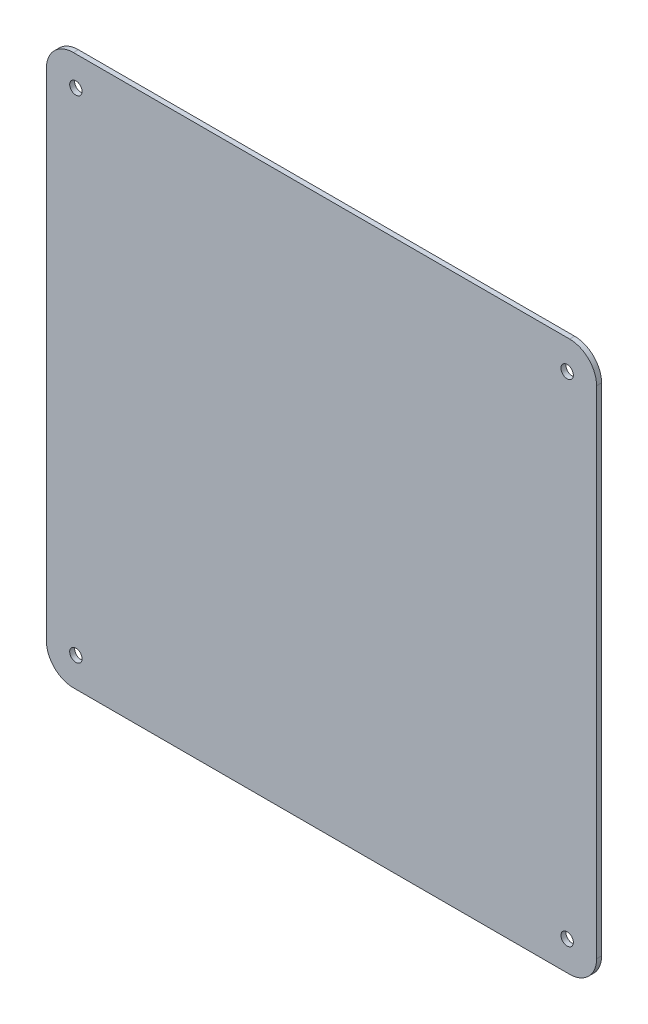
SolidWorks part; units mm, degrees
ref_plane "Piano frontale" through (0, 0, 0) normal (0, 0, 1) x (1, 0, 0)
ref_plane "Piano superiore" through (0, 0, 0) normal (0, 1, 0) x (1, 0, 0)
ref_plane "Piano destro" through (0, 0, 0) normal (1, 0, 0) x (0, 0, -1)
sketch "Sketch1" plane through (0, 0, 0) normal (0, 0, 1) x (1, 0, 0)
  line L4 (-80, 89.2) -> (80, 89.2) construction
  line L5 (89.2, 80) -> (89.2, -80) construction
  line L6 (80, -89.2) -> (-80, -89.2) construction
  line L7 (-89.2, -80) -> (-89.2, 80) construction
  line L8 (-80, 88.7) -> (80, 88.7)
  line L9 (88.7, 80) -> (88.7, -80)
  line L10 (80, -88.7) -> (-80, -88.7)
  line L11 (-88.7, -80) -> (-88.7, 80)
  arc A10 (-80, 89.2) -> (-89.2, 80) centre (-80, 80) ccw construction
  arc A13 (89.2, 80) -> (80, 89.2) centre (80, 80) ccw construction
  arc A14 (80, -89.2) -> (89.2, -80) centre (80, -80) ccw construction
  arc A15 (-89.2, -80) -> (-80, -89.2) centre (-80, -80) ccw construction
  arc A16 (88.7, 80) -> (80, 88.7) centre (80, 80) ccw
  arc A17 (80, -88.7) -> (88.7, -80) centre (80, -80) ccw
  arc A18 (-88.7, -80) -> (-80, -88.7) centre (-80, -80) ccw
  arc A19 (-80, 88.7) -> (-88.7, 80) centre (-80, 80) ccw
  dimension "D1" = 0.5
extrude "Boss-Extrude1" add sketch "Sketch1" along normal blind 1.6
hole_wizard "Ø4.0 (4) Diameter Hole1" positions "Sketch2" profile "Sketch3" hole size "Ø4.0" standard "ANSI Metric" end condition through all
sketch "Sketch2" plane through (0, 0, 0) normal (0, 0, -1) x (-1, 0, 0)
  point P0 (-79.2, 79.2)
  point P3 (79.2, 79.2)
  point P6 (-79.2, -79.2)
  point P9 (79.2, -79.2)
sketch "Sketch3" plane through (79.2, 79.2, 0) normal (1, 0, 0) x (0, 1, 0)
  line L0 (0, 0) -> (0, 1.6)
  line L1 (0, 1.6) -> (2, 1.6)
  line L2 (2, 1.6) -> (2, 0)
  line L5 (2, 0) -> (0, 0)
  line L11 (0, -6.35) -> (0, 107.95) construction
  dimension "Thru Hole Dia." = 4
  dimension "Thru Hole Depth" = 1.6
